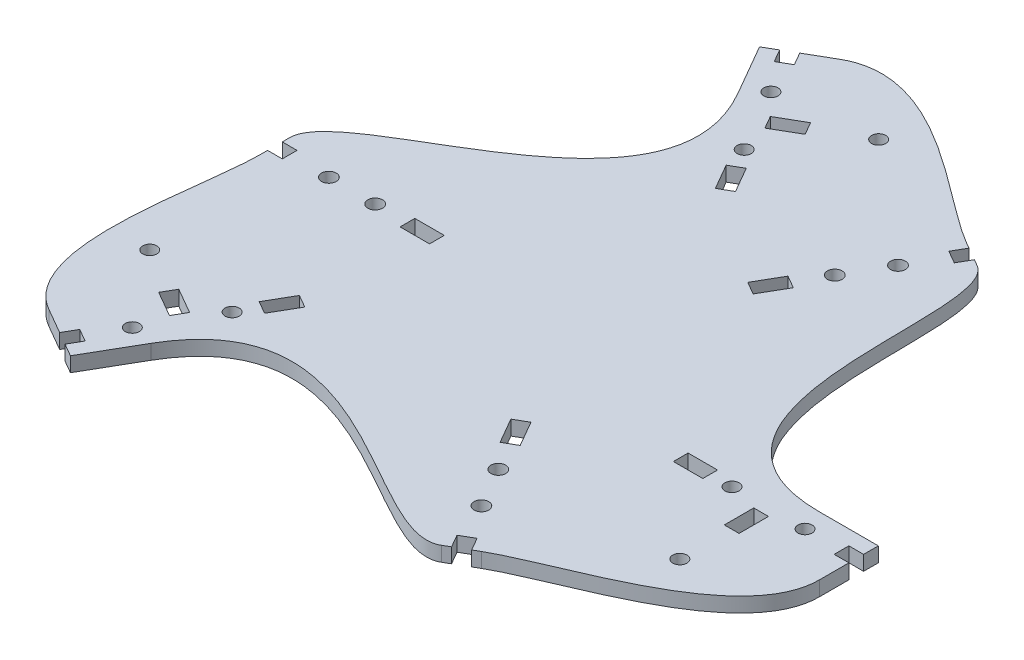
SolidWorks part; units mm, degrees
ref_plane "Front Plane" through (0, 0, 0) normal (0, 0, 1) x (1, 0, 0)
ref_plane "Top Plane" through (0, 0, 0) normal (0, 1, 0) x (1, 0, 0)
ref_plane "Right Plane" through (0, 0, 0) normal (1, 0, 0) x (0, 0, -1)
sketch "Sketch1" plane through (0, 0, 0) normal (0, 1, 0) x (1, 0, 0)
  line L0 (76.2, 0) -> (0, 0) construction
  line L1 (38.1, 65.9911) -> (0, 0) construction
  line L2 (-46.4039, -61.1969) -> (-49.1535, -59.6094)
  line L3 (76.2, -9.5885) -> (76.2, -12.7635)
  line L4 (15.6623, 23.9529) -> (18.8373, 29.4522)
  line L5 (15.6623, 23.9529) -> (12.9127, 25.5404)
  line L6 (-76.2, -989.805) -> (-76.2, 49010.195) construction
  line L7 (29.0004, 56.5801) -> (34.4996, 53.4051) construction
  line L8 (18.8373, 29.4522) -> (16.0877, 31.0397)
  line L9 (12.9127, 25.5404) -> (16.0877, 31.0397)
  line L10 (76.2, -9.5885) -> (63.5, -9.5885)
  line L11 (43.224, -48.3681) -> (25.8123, -58.4207) construction
  line L12 (37.2422, -9.5885) -> (88.1057, -9.5885) construction
  line L13 (-41.6479, -40.2593) -> (-43.2354, -43.0089)
  line L14 (15.6623, 23.9529) -> (16.0877, 31.0397) construction
  line L15 (18.8373, 29.4522) -> (12.9127, 25.5404) construction
  line L16 (76.2, -12.7635) -> (73.025, -12.7635)
  line L17 (38.354, -12.7635) -> (44.704, -12.7635)
  line L18 (38.354, -12.7635) -> (38.354, -15.9385)
  line L19 (38.354, -15.9385) -> (44.704, -15.9385)
  line L20 (44.704, -12.7635) -> (44.704, -15.9385)
  line L21 (38.354, -12.7635) -> (44.704, -15.9385) construction
  line L22 (38.354, -15.9385) -> (44.704, -12.7635) construction
  line L23 (73.025, -12.7635) -> (73.025, -15.9385)
  line L24 (73.025, -15.9385) -> (76.2, -15.9385)
  line L25 (38.354, -14.351) -> (73.025, -14.351) construction
  line L26 (76.2, -15.9385) -> (76.2, -22.2885)
  line L27 (30.3752, 55.7864) -> (28.7877, 53.0367)
  line L28 (28.7877, 53.0367) -> (31.5373, 51.4492)
  line L29 (31.5373, 51.4492) -> (33.1248, 54.1989)
  line L30 (29.0004, 56.5801) -> (30.3752, 55.7864)
  line L31 (33.1248, 54.1989) -> (34.4996, 53.4051)
  line L32 (76.2, -9.5885) -> (76.2, -22.2885) construction
  line L33 (12.9127, -25.5404) -> (16.0877, -31.0397)
  line L34 (12.9127, -25.5404) -> (15.6623, -23.9529)
  line L35 (16.0877, -31.0397) -> (18.8373, -29.4522)
  line L36 (15.6623, -23.9529) -> (18.8373, -29.4522)
  line L37 (-46.4039, -61.1969) -> (-40.0539, -50.1984)
  line L38 (-49.1535, -59.6094) -> (-47.566, -56.8598)
  line L39 (-30.2305, -26.8338) -> (-33.4055, -32.333)
  line L40 (-30.2305, -26.8338) -> (-32.9801, -25.2463)
  line L41 (-32.9801, -25.2463) -> (-36.1551, -30.7455)
  line L42 (-33.4055, -32.333) -> (-36.1551, -30.7455)
  line L43 (-47.566, -56.8598) -> (-50.3156, -55.2723)
  line L44 (-50.3156, -55.2723) -> (-51.9031, -58.0219)
  line L45 (-51.9031, -58.0219) -> (-57.4024, -54.8469)
  line L46 (33.1248, -54.1989) -> (31.5373, -51.4492)
  line L47 (31.5373, -51.4492) -> (28.7877, -53.0367)
  line L48 (28.7877, -53.0367) -> (30.3752, -55.7864)
  line L49 (34.4996, -53.4051) -> (33.1248, -54.1989)
  line L50 (30.3752, -55.7864) -> (29.0004, -56.5801)
  line L51 (-38.1, -65.9911) -> (0, 0) construction
  line L52 (38.1, -65.9911) -> (0, 0) construction
  line L53 (34.4996, -53.4051) -> (29.0004, -56.5801) construction
  line L54 (12.9127, -25.5404) -> (18.8373, -29.4522) construction
  line L55 (16.0877, -31.0397) -> (15.6623, -23.9529) construction
  line L56 (-30.2305, -26.8338) -> (-36.1551, -30.7455) construction
  line L57 (-32.9801, -25.2463) -> (-33.4055, -32.333) construction
  line L58 (-31.6053, -26.04) -> (-48.9408, -56.066) construction
  line L59 (-46.4039, -61.1969) -> (-57.4024, -54.8469) construction
  line L60 (-29.7961, 70.7854) -> (-27.0465, 72.3729)
  line L61 (-28.575, 1.5875) -> (-34.925, 1.5875)
  line L62 (-28.575, 1.5875) -> (-28.575, -1.5875)
  line L63 (-34.925, 1.5875) -> (-34.925, -1.5875)
  line L64 (-28.575, -1.5875) -> (-34.925, -1.5875)
  line L65 (-29.7961, 70.7854) -> (-23.4461, 59.7869)
  line L66 (-27.0465, 72.3729) -> (-25.459, 69.6233)
  line L67 (-8.1235, 39.5973) -> (-11.2985, 45.0965)
  line L68 (-8.1235, 39.5973) -> (-5.3739, 41.1848)
  line L69 (-5.3739, 41.1848) -> (-8.5489, 46.684)
  line L70 (-11.2985, 45.0965) -> (-8.5489, 46.684)
  line L71 (-25.459, 69.6233) -> (-22.7094, 71.2108)
  line L72 (-22.7094, 71.2108) -> (-24.2969, 73.9604)
  line L73 (-24.2969, 73.9604) -> (-18.7976, 77.1354)
  line L74 (-63.5, -1.5875) -> (-60.325, -1.5875)
  line L75 (-60.325, -1.5875) -> (-60.325, 1.5875)
  line L76 (-60.325, 1.5875) -> (-63.5, 1.5875)
  line L77 (-63.5, -3.175) -> (-63.5, -1.5875)
  line L78 (-63.5, 1.5875) -> (-63.5, 3.175)
  line L79 (-38.1, 65.9911) -> (0, 0) construction
  line L80 (-76.2, 0) -> (0, 0) construction
  line L81 (-63.5, -3.175) -> (-63.5, 3.175) construction
  line L82 (-28.575, 1.5875) -> (-34.925, -1.5875) construction
  line L83 (-34.925, 1.5875) -> (-28.575, -1.5875) construction
  line L84 (-8.1235, 39.5973) -> (-8.5489, 46.684) construction
  line L85 (-5.3739, 41.1848) -> (-11.2985, 45.0965) construction
  line L86 (-6.7487, 40.391) -> (-24.0842, 70.417) construction
  line L87 (-29.7961, 70.7854) -> (-18.7976, 77.1354) construction
  line L88 (55.6895, -15.9385) -> (58.8645, -15.9385)
  line L89 (55.6895, -15.9385) -> (55.6895, -22.2885)
  line L90 (55.6895, -22.2885) -> (58.8645, -22.2885)
  line L91 (58.8645, -15.9385) -> (58.8645, -22.2885)
  line L92 (-41.6479, -40.2593) -> (-47.1472, -37.0843)
  line L93 (-47.1472, -37.0843) -> (-48.7347, -39.8339)
  line L94 (-43.2354, -43.0089) -> (-48.7347, -39.8339)
  line L95 (-14.0416, 56.1978) -> (-15.6291, 58.9474)
  line L96 (-14.0416, 56.1978) -> (-8.5423, 59.3728)
  line L97 (-8.5423, 59.3728) -> (-10.1298, 62.1224)
  line L98 (-15.6291, 58.9474) -> (-10.1298, 62.1224)
  line L99 (76.2, 0.0013) -> (76.2, -38.0509) construction
  circle A0 centre (0, 0) radius 76.2 construction
  circle A1 centre (65.151, -14.351) radius 1.524
  circle A2 centre (49.403, -14.351) radius 1.524
  circle A3 centre (25.9334, 44.918) radius 1.5875
  circle A4 centre (20.9423, 36.2731) radius 1.5875
  circle A5 centre (-45.0038, -49.2469) radius 1.524
  circle A6 centre (-37.1298, -35.6088) radius 1.524
  circle A7 centre (25.9334, -44.918) radius 1.5875
  circle A8 centre (20.9423, -36.2731) radius 1.5875
  circle A9 centre (-20.1472, 63.5979) radius 1.524
  circle A10 centre (-12.2732, 49.9598) radius 1.524
  circle A11 centre (-51.8668, 0) radius 1.5875
  circle A12 centre (-41.8846, 0) radius 1.5875
  circle A13 centre (57.277, -33.4645) radius 1.524
  circle A14 centre (-57.6196, -32.8711) radius 1.524
  circle A15 centre (0.3426, 66.3356) radius 1.524
  spline S0 degree 3 poles (63.5, -9.5885) (26.0624, -9.5885) (45.6203, 46.9846) (34.4996, 53.4051) knots 0 0 0 0 1 1 1 1
  spline S1 degree 3 poles (-63.5, -3.175) (-63.5, -15.7408) (-71.9494, -46.4482) (-57.4024, -54.8469) knots 0 0 0 0 1 1 1 1
  spline S2 degree 3 poles (-40.0539, -50.1984) (-21.3351, -17.7764) (17.8797, -63.0006) (29.0004, -56.5801) knots 0 0 0 0 1 1 1 1
  spline S3 degree 3 poles (34.4996, -53.4051) (45.3819, -47.1222) (76.2, -39.0859) (76.2, -22.2885) knots 0 0 0 0 1 1 1 1
  spline S4 degree 3 poles (-23.4461, 59.7869) (-4.7273, 27.3649) (-63.5, 16.016) (-63.5, 3.175) knots 0 0 0 0 1 1 1 1
  spline S5 degree 3 poles (29.0004, 56.5801) (18.1181, 62.863) (-4.2506, 85.5341) (-18.7976, 77.1354) knots 0 0 0 0 1 1 1 1
  point P12 (15.875, 27.4963)
  point P19 (31.75, 54.9926)
  point P31 (41.529, -14.351)
  point P48 (30.1625, 52.243)
  point P60 (15.875, -27.4963)
  point P70 (-33.1928, -28.7897)
  point P95 (57.277, -22.2885)
  point P98 (-31.75, 0)
  point P108 (-8.3362, 43.1407)
  dimension "D1" = 152.4
  dimension "D4" = 12.7
  dimension "D5" = 9.5885
  dimension "D11" = 3.175
  dimension "D19" = 3.048
  dimension "D22" = 3.175
  dimension "D25" = 3.048
  dimension "D2" = 60
  dimension "D3" = 3
  dimension "D6" = 3.175
  dimension "D7" = 6.35
  dimension "D8" = 63.5
  dimension "D9" = 6.35
  dimension "D10" = 12.7
  dimension "D12" = 3.175
  dimension "D13" = 28.321
  dimension "D14" = 6.35
  dimension "D15" = 3.175
  dimension "D16" = 3.175
  dimension "D17" = 4.699
  dimension "D18" = 15.748
  dimension "D20" = 3.175
  dimension "D21" = 25.4
  dimension "D23" = 8.4582
  dimension "D24" = 9.9822
  dimension "D26" = 6.35
  dimension "D27" = 3.175
  dimension "D28" = 15.748
  dimension "D29" = 11.176
  dimension "D30" = 3
extrude "Boss-Extrude1" add sketch "Sketch1" along normal blind 3.175
